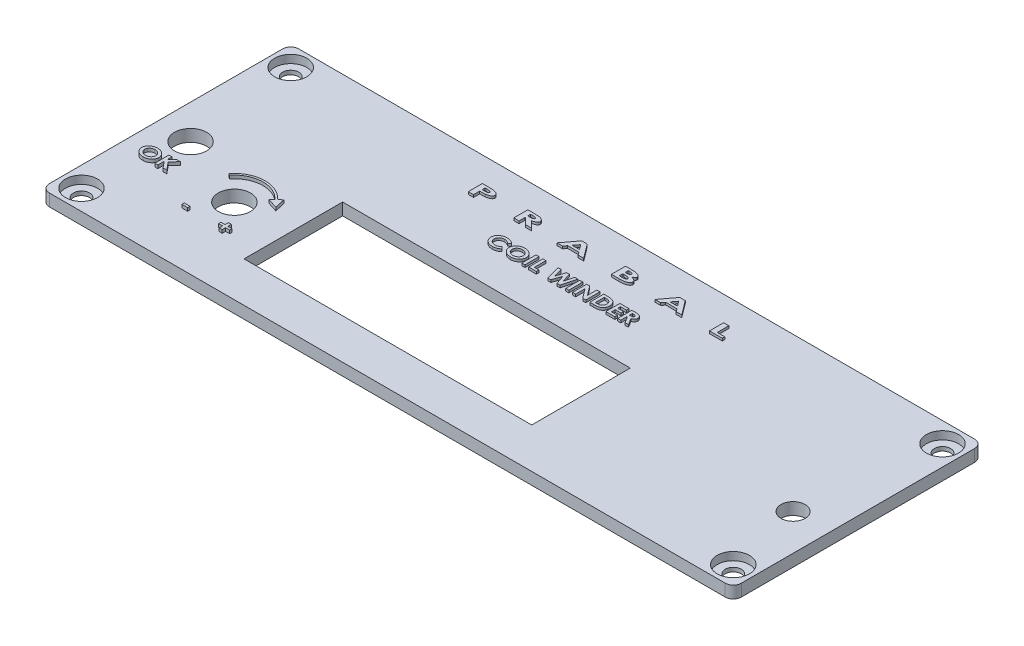
SolidWorks part; units mm, degrees
ref_plane "Front Plane" through (0, 0, 0) normal (0, 0, 1) x (1, 0, 0)
ref_plane "Top Plane" through (0, 0, 0) normal (0, 1, 0) x (1, 0, 0)
ref_plane "Right Plane" through (0, 0, 0) normal (1, 0, 0) x (0, 0, -1)
sketch "Sketch1" plane through (0, 0, 0) normal (0, 1, 0) x (1, 0, 0)
  line L0 (86, -29) -> (86, 29)
  line L1 (84, 31) -> (-84, 31)
  line L2 (-86, 29) -> (-86, -29)
  line L3 (-84, -31) -> (84, -31)
  line L4 (0, 0) -> (0, 52.062) construction
  line L5 (4.5382, 0) -> (0, 0) construction
  line L6 (0, 0) -> (108.3149, 0) construction
  arc A0 (84, -31) -> (86, -29) centre (84, -29) ccw
  arc A1 (86, 29) -> (84, 31) centre (84, 29) ccw
  arc A2 (-84, 31) -> (-86, 29) centre (-84, 29) ccw
  arc A3 (-86, -29) -> (-84, -31) centre (-84, -29) ccw
  circle A4 centre (81, 26) radius 2
  circle A5 centre (81, -26) radius 2
  circle A6 centre (-81, -26) radius 2
  circle A7 centre (-81, 26) radius 2
  dimension "D5" = 2
  dimension "D6" = 2
  dimension "D7" = 4
  dimension "D8" = 2
  dimension "D9" = 4
  dimension "D10" = 4
  dimension "D11" = 4
  dimension "D12" = 2
  dimension "D1" = 62
  dimension "D2" = 172
  dimension "D3" = 5
  dimension "D4" = 5
  dimension "D13" = 5
  dimension "D14" = 5
  dimension "D15" = 5
  dimension "D16" = 5
  dimension "D17" = 5
  dimension "D18" = 5
  dimension "D19" = 2
extrude "Boss-Extrude1" add sketch "Sketch1" along normal blind 3
sketch "Sketch2" plane through (0, 3, 0) normal (0, 1, 0) x (1, 0, 0)
  circle A0 centre (-81, 26) radius 4
  circle A1 centre (81, 26) radius 4
  circle A2 centre (-81, -26) radius 4
  circle A4 centre (81, -26) radius 4
  dimension "D1" = 8
  dimension "D2" = 8
  dimension "D3" = 8
  dimension "D4" = 8
extrude "Cut-Extrude1" cut sketch "Sketch2" against normal blind 2
sketch "Sketch3" plane through (0, 3, 0) normal (0, 1, 0) x (1, 0, 0)
  line L0 (-84, -31) -> (84, -31) construction
  line L1 (-86, 29) -> (-86, -29) construction
  line L3 (-45.6, 3.5) -> (25.9, 3.5)
  line L4 (-45.6, 3.5) -> (-45.6, -21)
  line L5 (-45.6, -21) -> (25.9, -21)
  line L6 (25.9, 3.5) -> (25.9, -21)
  line L7 (-45.6, 3.5) -> (25.9, -21) construction
  line L8 (-45.6, -21) -> (25.9, 3.5) construction
  circle A0 centre (-77.5, -2.4) radius 4
  circle A1 centre (-59, -10) radius 4
  circle A2 centre (76.9917, -7.1289) radius 3
  point P8 (-9.85, -8.75)
  dimension "D2" = 8
  dimension "D6" = 8
  dimension "D11" = 6
  dimension "D1" = 28.6
  dimension "D3" = 8.5
  dimension "D4" = 27
  dimension "D5" = 21
  dimension "D7" = 10
  dimension "D8" = 24.5
  dimension "D9" = 71.5
  dimension "D10" = 40.4
extrude "Cut-Extrude2" cut sketch "Sketch3" against normal blind 12
sketch "Sketch4" plane through (0, 3, 0) normal (0, 1, 0) x (1, 0, 0)
  line L0 (-84.4833, -12.2962) -> (-70.7402, -12.2962) construction
  line L1 (-66.3884, -18.7615) -> (-53.0851, -18.7615) construction
  line L4 (-51.9884, -6.7249) -> (-52.5566, -4.1282)
  line L5 (-52.5566, -4.1282) -> (-53.3593, -4.8598)
  line L6 (-54.5212, -5.9186) -> (-51.9884, -6.7249)
  line L7 (-65.0166, -5.3054) -> (-64.6224, -5.6129)
  line L8 (-53.7289, -5.1965) -> (-54.5212, -5.9186)
  line L9 (-59, -10) -> (-52.3347, -3.926) construction
  arc A0 (-64.6224, -5.6129) -> (-53.7289, -5.1965) centre (-59, -10) cw
  circle A1 centre (-59, -10) radius 4 construction
  arc A2 (-65.0166, -5.3054) -> (-53.3593, -4.8598) centre (-59, -10) cw
  arc A3 (-64.6224, -5.6129) -> (-53.7289, -5.1965) centre (-59, -10) cw construction
  text T0 "<b>OK</b>" font "Century Gothic" height 3.5
  text T1 "<b> -    +</b>" font "Century Gothic" height 3.5
  dimension "D1" = 60
  dimension "D2" = 60
  dimension "D3" = 0.5
extrude "Boss-Extrude2" add sketch "Sketch4" along normal blind 0.8
sketch "Sketch6" plane through (0, 3, 0) normal (0, 1, 0) x (1, 0, 0)
  line L0 (-48.2569, 20.7468) -> (48.2569, 20.7468) construction
  line L1 (0, 0) -> (0, 56.3911) construction
  line L2 (-48.2569, 12.0333) -> (48.2569, 12.0333) construction
  text T0 "<b>PRABAL</b>" font "Century Gothic" height 3.5
  text T1 "<b>COIL WINDER </b>" font "Century Gothic" height 3.5
extrude "Boss-Extrude3" add sketch "Sketch6" along normal blind 0.6
